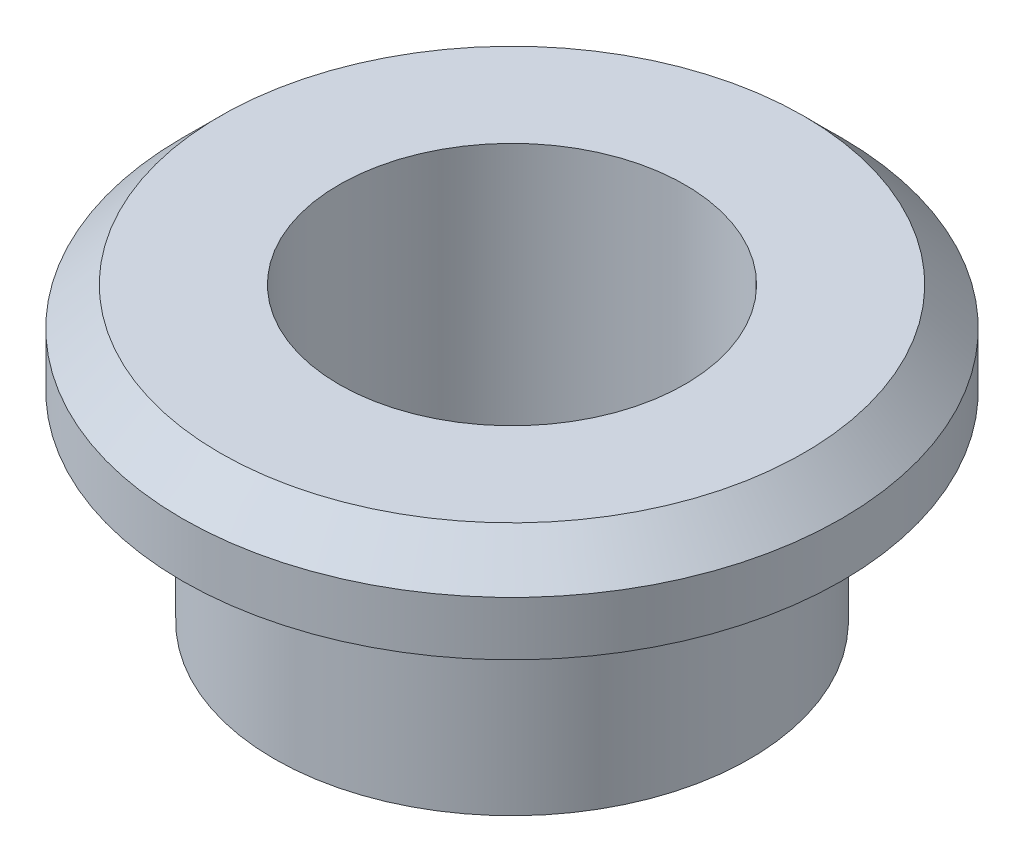
SolidWorks part; units mm, degrees
material "High-leaded brass, UNS C34200"
ref_plane "Front Plane" through (0, 0, 0) normal (0, 0, 1) x (1, 0, 0)
ref_plane "Top Plane" through (0, 0, 0) normal (0, 1, 0) x (1, 0, 0)
ref_plane "Right Plane" through (0, 0, 0) normal (1, 0, 0) x (0, 0, -1)
sketch "Sketch1" plane through (0, 0, 0) normal (0, 0, 1) x (1, 0, 0)
  line L0 (0, 9.7911) -> (0, 0) construction
  line L1 (1.6, 2.7) -> (1.6, 0)
  line L2 (1.6, 0) -> (2.2, 0)
  line L3 (2.2, 0) -> (2.2, 1.85)
  line L4 (2.2, 1.85) -> (3.05, 1.85)
  line L5 (3.05, 1.85) -> (3.05, 2.35)
  line L6 (3.05, 2.35) -> (2.7, 2.7)
  line L7 (2.7, 2.7) -> (1.6, 2.7)
  dimension "D1" = 1.6
  dimension "D2" = 3.05
  dimension "D3" = 1.85
  dimension "D4" = 0.85
  dimension "D5" = 135
  dimension "D6" = 0.35
  dimension "D7" = 2.2
revolve "Revolve1" add sketch "Sketch1" angle 360 about L0
